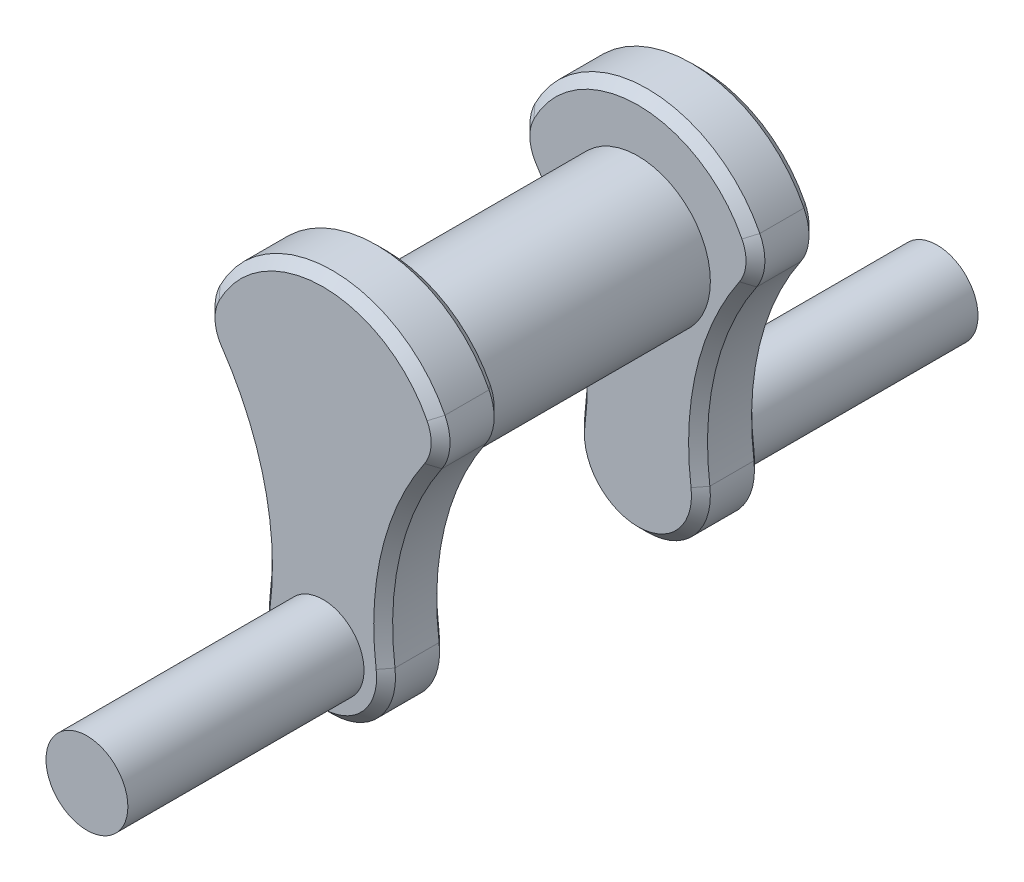
SolidWorks part; units mm, degrees
material "AISI 1020"
ref_plane "Front Plane" through (0, 0, 0) normal (0, 0, 1) x (1, 0, 0)
ref_plane "Top Plane" through (0, 0, 0) normal (0, 1, 0) x (1, 0, 0)
ref_plane "Right Plane" through (0, 0, 0) normal (1, 0, 0) x (0, 0, -1)
sketch "Sketch1" plane through (0, 0, 0) normal (0, 0, 1) x (1, 0, 0)
  circle A0 centre (0, 0) radius 23
  dimension "D1" = 46
extrude "Boss-Extrude1" add sketch "Sketch1" along normal mid plane 80
sketch "Sketch2" plane through (0, 0, 40) normal (0, 0, 1) x (1, 0, 0)
  line L0 (0, 0) -> (58.5567, 12.9817) construction
  line L1 (0, 0) -> (-58.5567, 12.9817) construction
  line L2 (0, 53.051) -> (0, -94.0928) construction
  arc A0 (39.0518, 8.6576) -> (-39.0518, 8.6576) centre (0, 0) ccw
  arc A1 (-19.8342, -59.4302) -> (19.8342, -59.4302) centre (0, -62) ccw
  arc A2 (-39.0518, 8.6576) -> (-19.8342, -59.4302) centre (-109.0882, -47.866) cw
  arc A3 (19.8342, -59.4302) -> (39.0518, 8.6576) centre (109.0882, -47.866) cw
  dimension "D1" = 80
  dimension "D2" = 40
  dimension "D5" = 90
  dimension "D3" = 62
  dimension "D4" = 155
extrude "Boss-Extrude2" add sketch "Sketch2" along normal blind 20
sketch "Sketch3" plane through (0, 0, 60) normal (0, 0, 1) x (1, 0, 0)
  circle A0 centre (0, -62) radius 13
  dimension "D1" = 26
extrude "Boss-Extrude3" add sketch "Sketch3" along normal blind 75
fillet "Fillet1" radius 15 2 edges at (-39.0518, 8.6576, 50) (39.0518, 8.6576, 50)
chamfer "Chamfer2" distance 3 angle 45 12 edges at (-37.2873, 10.2819, 40) (-21.5548, -26.9399, 40) (0, 40, 40) (0, -82, 40) (37.2873, 10.2819, 40) (21.5548, -26.9399, 40) (0, -82, 60) (21.5548, -26.9399, 60) (-21.5548, -26.9399, 60) (37.2873, 10.2819, 60) (-37.2873, 10.2819, 60) (0, 40, 60)
mirror "Mirror1" about plane through (0, 0, 0) normal (0, 0, 1) of "Chamfer2", "Boss-Extrude3", "Boss-Extrude2", "Fillet1"
